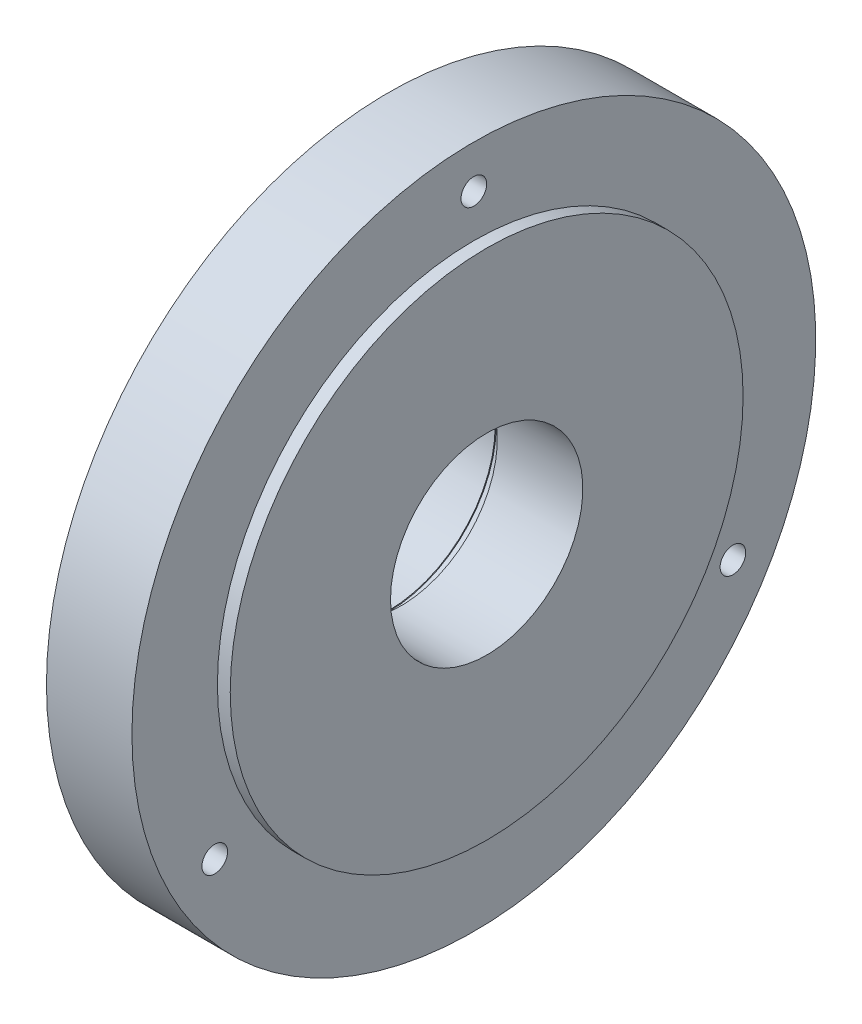
SolidWorks part; units mm, degrees
ref_plane "Front Plane" through (0, 0, 0) normal (0, 0, 1) x (1, 0, 0)
ref_plane "Top Plane" through (0, 0, 0) normal (0, 1, 0) x (1, 0, 0)
ref_plane "Right Plane" through (0, 0, 0) normal (1, 0, 0) x (0, 0, -1)
sketch "Sketch1" plane through (0, 0, 0) normal (0, 0, 1) x (1, 0, 0)
  line L0 (0, 22.5) -> (-20, 22.5)
  line L1 (-20, 22.5) -> (-20, 25.25)
  line L2 (-20, 25.25) -> (-23, 25.25)
  line L3 (-23, 25.25) -> (-23, 25)
  line L4 (-23, 25) -> (-47, 25)
  line L5 (-47, 25) -> (-47, 25.25)
  line L6 (-47, 25.25) -> (-53, 25.25)
  line L7 (-53, 25.25) -> (-53, 37.5)
  line L8 (-53, 37.5) -> (-23, 37.5)
  line L9 (-23, 37.5) -> (-23, 80)
  line L10 (-23, 80) -> (-3, 80)
  line L11 (-3, 80) -> (-3, 60)
  line L12 (-3, 60) -> (0, 60)
  line L13 (0, 60) -> (0, 22.5)
  line L14 (-1000, 0) -> (49000, 0) construction
  dimension "D1" = 20
  dimension "D2" = 22.5
  dimension "D3" = 25.25
  dimension "D4" = 3
  dimension "D5" = 25
  dimension "D6" = 53
  dimension "D7" = 6
  dimension "D8" = 37.5
  dimension "D9" = 80
  dimension "D10" = 60
revolve "Revolve1" add sketch "Sketch1" angle 360 about L14
fillet "Fillet1" radius 6 1 edges at (-23, 0, 37.5)
sketch "Sketch2" plane through (-3, 0, 0) normal (1, 0, 0) x (0, 0, -1)
  circle A0 centre (0, 0) radius 70 construction
  circle A1 centre (0, 70) radius 3
  circle A2 centre (60.6218, -35) radius 3
  circle A3 centre (-60.6218, -35) radius 3
  point P11 (0, 0)
  dimension "D1" = 3
extrude "Cut-Extrude1" cut sketch "Sketch2" against normal through all
